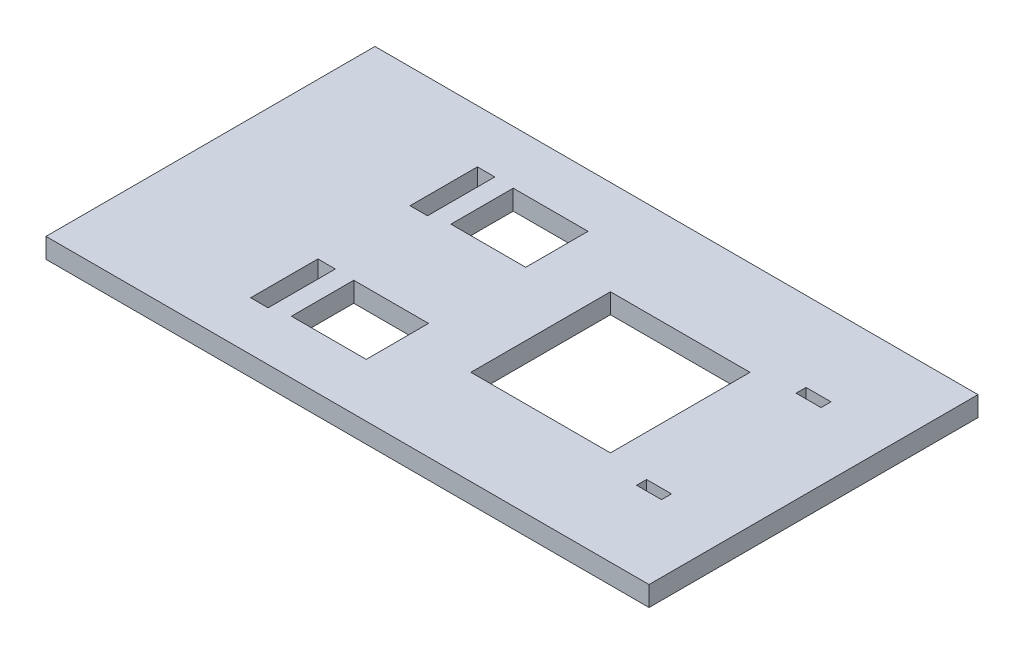
SolidWorks part; units mm, degrees
material "Maple"
ref_plane "Front Plane" through (0, 0, 0) normal (0, 0, 1) x (1, 0, 0)
ref_plane "Top Plane" through (0, 0, 0) normal (0, 1, 0) x (1, 0, 0)
ref_plane "Right Plane" through (0, 0, 0) normal (1, 0, 0) x (0, 0, -1)
sketch "Sketch1" plane through (0, 0, 0) normal (0, 1, 0) x (1, 0, 0)
  line L1 (0, 0) -> (121, 0)
  line L2 (0, 0) -> (0, -66)
  line L3 (0, -66) -> (121, -66)
  line L4 (121, 0) -> (121, -66)
  dimension "D1" = 121
  dimension "D2" = 66
extrude "Boss-Extrude1" add sketch "Sketch1" along normal blind 4
sketch "Sketch2" plane through (0, 4, 0) normal (0, 1, 0) x (1, 0, 0)
  line L0 (0, -33) -> (121, -33) construction
  line L1 (0, 0) -> (0, -66) construction
  line L2 (121, -66) -> (121, 0) construction
  line L3 (46, 0) -> (46, -66) construction
  line L4 (121, 0) -> (0, 0) construction
  line L5 (0, -66) -> (121, -66) construction
  line L7 (66.25, -19) -> (94.25, -19)
  line L8 (66.25, -19) -> (66.25, -47)
  line L9 (66.25, -47) -> (94.25, -47)
  line L10 (94.25, -19) -> (94.25, -47)
  line L11 (66.25, -19) -> (94.25, -47) construction
  line L12 (66.25, -47) -> (94.25, -19) construction
  line L13 (38.5, -23.25) -> (53.5, -23.25)
  line L14 (38.5, -23.25) -> (38.5, -10.75)
  line L15 (38.5, -10.75) -> (53.5, -10.75)
  line L16 (53.5, -23.25) -> (53.5, -10.75)
  line L17 (38.5, -23.25) -> (53.5, -10.75) construction
  line L18 (38.5, -10.75) -> (53.5, -23.25) construction
  line L19 (38.5, -55.25) -> (53.5, -55.25)
  line L20 (38.5, -55.25) -> (38.5, -42.75)
  line L21 (38.5, -42.75) -> (53.5, -42.75)
  line L22 (53.5, -55.25) -> (53.5, -42.75)
  line L23 (38.5, -55.25) -> (53.5, -42.75) construction
  line L24 (38.5, -42.75) -> (53.5, -55.25) construction
  circle A0 centre (46, -17) radius 3.5 construction
  circle A1 centre (46, -49) radius 3.5 construction
  point P16 (80.25, -33)
  dimension "D1" = 7
  dimension "D2" = 32
  dimension "D3" = 16
  dimension "D4" = 46
  dimension "D5" = 28
  dimension "D6" = 28
  dimension "D7" = 40.75
  dimension "D8" = 12.5
  dimension "D9" = 15
  dimension "D10" = 15
  dimension "D11" = 12.5
extrude "Cut-Extrude1" cut sketch "Sketch2" against normal through all
sketch "Sketch3" plane through (0, 0, 0) normal (0, -1, 0) x (1, 0, 0)
  line L1 (107.5, 50) -> (102.5, 50)
  line L2 (107.5, 50) -> (107.5, 48)
  line L3 (107.5, 48) -> (102.5, 48)
  line L4 (102.5, 50) -> (102.5, 48)
  line L5 (102.5, 16) -> (107.5, 16)
  line L6 (102.5, 16) -> (102.5, 18)
  line L7 (102.5, 18) -> (107.5, 18)
  line L8 (107.5, 16) -> (107.5, 18)
extrude "Cut-Extrude2" cut sketch "Sketch3" against normal through all
sketch "Sketch4" plane through (0, 4, 0) normal (0, 1, 0) x (1, 0, 0)
  line L0 (38.5, -42.75) -> (38.5, -55.25) construction
  line L1 (31.2, -42.6459) -> (34.7, -42.6459)
  line L2 (31.2, -42.6459) -> (31.2, -56.1459)
  line L3 (31.2, -56.1459) -> (34.7, -56.1459)
  line L4 (34.7, -42.6459) -> (34.7, -56.1459)
  line L5 (31.2, -10.6496) -> (34.7, -10.6496)
  line L6 (31.2, -10.6496) -> (31.2, -24.1496)
  line L7 (31.2, -24.1496) -> (34.7, -24.1496)
  line L8 (34.7, -10.6496) -> (34.7, -24.1496)
  line L9 (38.5, -55.25) -> (53.5, -55.25) construction
  line L10 (38.5, -23.25) -> (53.5, -23.25) construction
  dimension "D1" = 13.5
  dimension "D2" = 3.5
  dimension "D3" = 3.8
  dimension "D4" = 0.8959
  dimension "D5" = 0.8996
  dimension "D6" = 13.5
extrude "Cut-Extrude3" cut sketch "Sketch4" against normal through all
equation "\"D3@Sketch2\"=\"D2@Sketch2\"/2"
equation "\"D11@Sketch2\"=\"D8@Sketch2\""
equation "\"D10@Sketch2\"=\"D9@Sketch2\""
